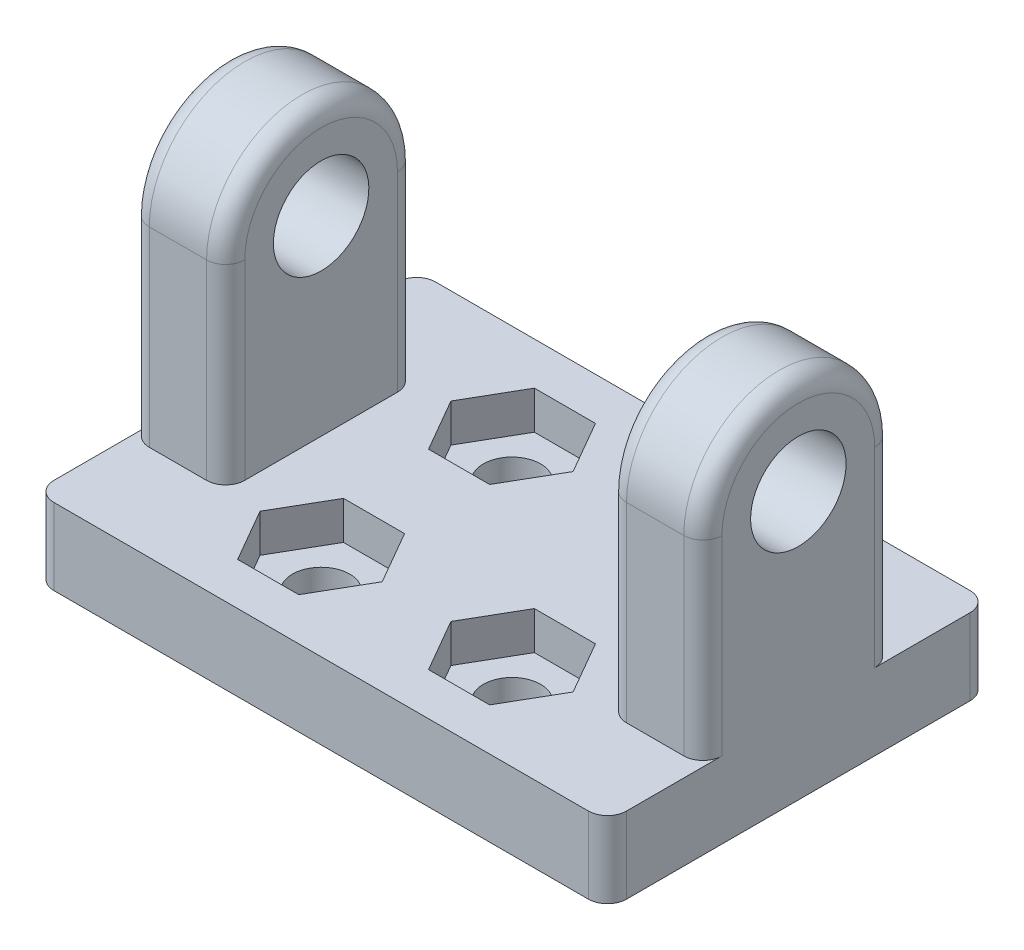
SolidWorks part; units mm, degrees
ref_plane "Plan de face" through (0, 0, 0) normal (0, 0, 1) x (1, 0, 0)
ref_plane "Plan de dessus" through (0, 0, 0) normal (0, 1, 0) x (1, 0, 0)
ref_plane "Plan de droite" through (0, 0, 0) normal (1, 0, 0) x (0, 0, -1)
sketch "Esquisse2" plane through (0, 0, 0) normal (1, 0, 0) x (0, 0, -1)
  line L0 (5, 0) -> (5, -10)
  line L2 (-5, 0) -> (-5, -10)
  line L3 (-5, -10) -> (5, -10)
  circle A0 centre (0, 0) radius 2.5
  arc A2 (5, 0) -> (-5, 0) centre (0, 0) ccw
  dimension "D1" = 5
  dimension "D2" = 10
  dimension "D3" = 5
  dimension "D4" = 5
extrude "Boss.-Extru.1" add sketch "Esquisse2" along normal mid plane 30
sketch "Esquisse4" plane through (0, -10, 0) normal (0, -1, 0) x (1, 0, 0)
  line L0 (-15, 5) -> (-15, -5) construction
  line L1 (-15, -10) -> (15, -10)
  line L2 (-15, -10) -> (-15, 10)
  line L3 (-15, 10) -> (15, 10)
  line L4 (15, -10) -> (15, 10)
  line L5 (15, 5) -> (15, -5) construction
  dimension "D1" = 20
  dimension "D4" = 10
extrude "Boss.-Extru.2" add sketch "Esquisse4" along normal blind 4
sketch "Esquisse5" plane through (0, -10, 0) normal (0, 1, 0) x (1, 0, 0)
  circle A0 centre (5, -5) radius 1.5
  circle A1 centre (5, 5) radius 1.5
  circle A2 centre (-5, 5) radius 1.5
  circle A3 centre (-5, -5) radius 1.5
  point P15 (0, 0)
  dimension "D1" = 3
  dimension "D2" = 10
  dimension "D3" = 10
  dimension "D4" = 5
  dimension "D5" = 5
extrude "Enlèv. mat.-Extru.1" cut sketch "Esquisse5" against normal up to next contours A0
sketch "Esquisse6" plane through (0, 0, 5) normal (0, 0, 1) x (1, 0, 0)
  line L0 (15, -10) -> (6.5, -10) construction
  line L1 (-10, 11.5437) -> (10, 11.5437)
  line L2 (-10, 11.5437) -> (-10, -10)
  line L3 (-10, -10) -> (10, -10)
  line L4 (10, 11.5437) -> (10, -10)
  line L5 (15, 0) -> (-15, 0) construction
  point P7 (0, 11.5437)
  point P8 (0, 0)
  point P11 (0, 0)
  dimension "D2" = 20
extrude "Enlèv. mat.-Extru.2" cut sketch "Esquisse6" against normal through all
sketch "Esquisse7" plane through (0, -10, 0) normal (0, 1, 0) x (1, 0, 0)
  line L8 (-1.8, -5) -> (-3.4, -2.2287)
  line L9 (-3.4, -2.2287) -> (-6.6, -2.2287)
  line L10 (-6.6, -2.2287) -> (-8.2, -5)
  line L11 (-8.2, -5) -> (-6.6, -7.7713)
  line L12 (-6.6, -7.7713) -> (-3.4, -7.7713)
  line L13 (-3.4, -7.7713) -> (-1.8, -5)
  line L14 (8.2, -5) -> (6.6, -2.2287)
  line L15 (6.6, -2.2287) -> (3.4, -2.2287)
  line L16 (3.4, -2.2287) -> (1.8, -5)
  line L17 (1.8, -5) -> (3.4, -7.7713)
  line L18 (3.4, -7.7713) -> (6.6, -7.7713)
  line L19 (6.6, -7.7713) -> (8.2, -5)
  line L20 (8.2, 5) -> (6.6, 7.7713)
  line L21 (6.6, 7.7713) -> (3.4, 7.7713)
  line L22 (3.4, 7.7713) -> (1.8, 5)
  line L23 (1.8, 5) -> (3.4, 2.2287)
  line L24 (3.4, 2.2287) -> (6.6, 2.2287)
  line L25 (6.6, 2.2287) -> (8.2, 5)
  line L26 (-1.8, 5) -> (-3.4, 7.7713)
  line L27 (-3.4, 7.7713) -> (-6.6, 7.7713)
  line L28 (-6.6, 7.7713) -> (-8.2, 5)
  line L29 (-8.2, 5) -> (-6.6, 2.2287)
  line L30 (-6.6, 2.2287) -> (-3.4, 2.2287)
  line L31 (-3.4, 2.2287) -> (-1.8, 5)
  line L32 (-15, 10) -> (15, 10) construction
  line L33 (15, -10) -> (-15, -10) construction
  circle A5 centre (-5, -5) radius 2.7713 construction
  circle A6 centre (5, -5) radius 2.7713 construction
  circle A7 centre (5, 5) radius 2.7713 construction
  circle A8 centre (-5, 5) radius 2.7713 construction
  dimension "D1" = 3.2
  dimension "D2" = 3.2
  dimension "D3" = 3.2
  dimension "D4" = 3.2
extrude "Enlèv. mat.-Extru.3" cut sketch "Esquisse7" against normal blind 2 and the other way through all
fillet "Congé1" radius 1 16 edges at (10, -5, -5) (10, -5, 5) (-10, -5, 5) (-10, -5, -5) (15, -5, -5) (15, -5, 5) (-15, -5, -5) (-15, -5, 5) (10, 5, 0) (-10, 5, 0) (15, 5, 0) (-15, 5, 0) (-15, -12, -10) (-15, -12, 10) (15, -12, -10) (15, -12, 10)
